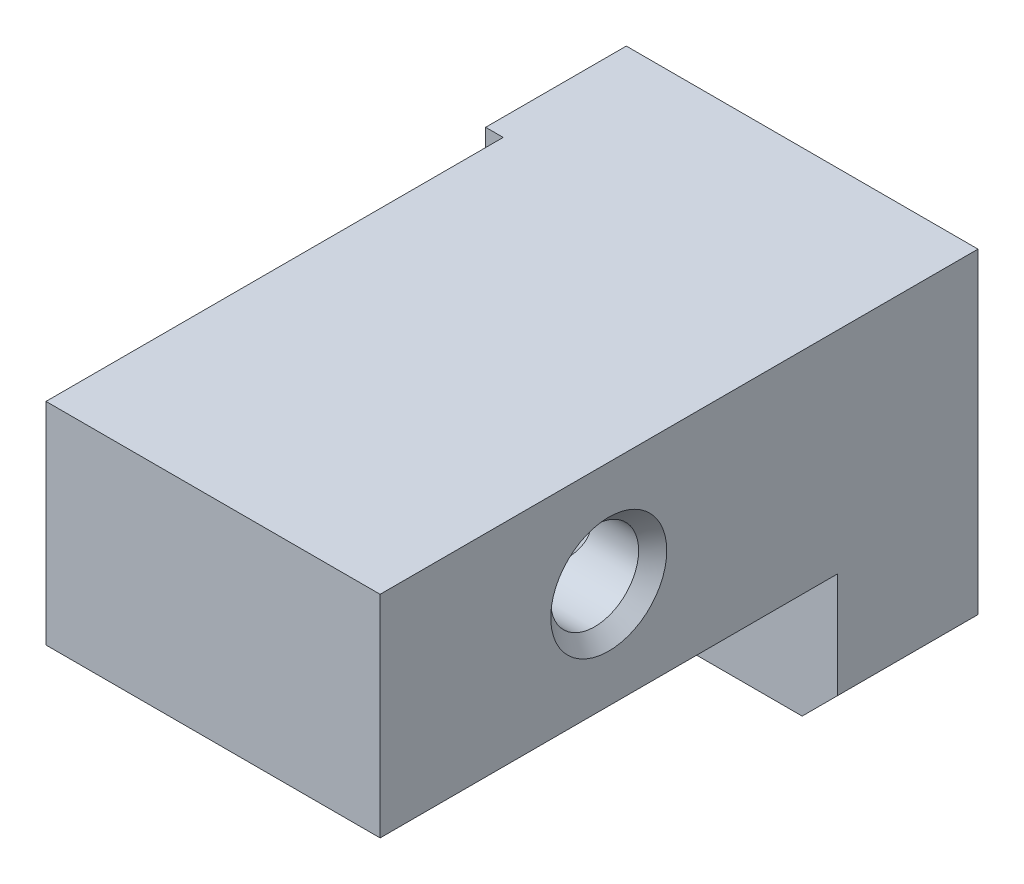
SolidWorks part; units mm, degrees
material "2024-T4"
ref_plane "Спереди" through (0, 0, 0) normal (0, 0, 1) x (1, 0, 0)
ref_plane "Сверху" through (0, 0, 0) normal (0, 1, 0) x (1, 0, 0)
ref_plane "Справа" through (0, 0, 0) normal (1, 0, 0) x (0, 0, -1)
sketch "Эскиз1" plane through (0, 0, 0) normal (0, 0, 1) x (1, 0, 0)
  line L1 (0, 0) -> (10, 0)
  line L2 (0, 0) -> (0, 10)
  line L3 (0, 10) -> (10, 10)
  line L4 (10, 0) -> (10, 10)
  dimension "D1" = 10
  dimension "D2" = 10
extrude "Бобышка-Вытянуть1" add sketch "Эскиз1" along normal blind 17
sketch "Эскиз7" plane through (0, 0, 17) normal (0, 0, 1) x (1, 0, 0)
  line L0 (0.5, 10) -> (0.5, 4)
  line L1 (10, 10) -> (0, 10) construction
  line L2 (0.5, 4) -> (10, 4)
  line L3 (10, 0) -> (10, 10) construction
  dimension "D1" = 9.5
  dimension "D2" = 6
extrude "Вырез-Вытянуть1" cut sketch "Эскиз7" against normal offset from surface (13 mm away) 4
hole_wizard "Отверстие обработанное метчиком M31" positions "Эскиз4" profile "Эскиз3" tap size "M3" standard "DIN" end condition through all
sketch "Эскиз4" plane through (10, 12.8478, -4.2017) normal (1, 0, 0) x (0, 0, 1)
  line L3 (4.2017, 2.8478) -> (4.2017, 12.8478) construction
  line L5 (21.2017, 2.8478) -> (4.2017, 2.8478) construction
  point P0 (14.7017, 5.8478)
  dimension "D1" = 10.5
  dimension "D2" = 3
sketch "Эскиз3" plane through (10, 7, 10.5) normal (0, 1, 0) x (0, 0, -1)
  line L0 (0, 0) -> (0, 9.5)
  line L1 (0, 9.5) -> (1.65, 9.5)
  line L2 (1.25, 9.1) -> (1.25, 0.4)
  line L3 (1.25, 0.4) -> (1.65, 0)
  line L5 (1.65, 0) -> (0, 0)
  line L6 (-1.25, 0.4) -> (-1.65, 0) construction
  line L7 (1.65, 9.5) -> (1.25, 9.1)
  line L8 (-1.65, 9.5) -> (-1.25, 9.1) construction
  line L11 (0, -6.35) -> (0, 107.95) construction
  dimension "Диаметр резьбы" = 2.5
  dimension "Глубина проходного сверла" = 9.5
  dimension "Диаметр передней зенковки" = 3.3
  dimension "Угол передней зенковки" = 90
  dimension "Диаметр задней зенковки" = 3.3
  dimension "Угол задней зенковки" = 90
hole_wizard "Отверстие обработанное метчиком M32" positions "Эскиз6" profile "Эскиз5" tap size "M3" standard "DIN"
sketch "Эскиз6" plane through (0, 0, 0) normal (0, 0, -1) x (-1, 0, 0)
  line L3 (0, 10) -> (0, 0) construction
  line L4 (0, 0) -> (-10, 0) construction
  point P0 (-3, 3)
  point P1 (-7, 7)
  dimension "D1" = 3
  dimension "D2" = 4
  dimension "D3" = 3
  dimension "D4" = 4
sketch "Эскиз5" plane through (3, 3, 0) normal (1, 0, 0) x (0, 1, 0)
  line L0 (0, 0) -> (0, 11.2511)
  line L1 (0, 11.2511) -> (1.25, 10.5)
  line L2 (1.25, 10.5) -> (1.25, 0.4)
  line L3 (1.25, 0.4) -> (1.65, 0)
  line L5 (1.65, 0) -> (0, 0)
  line L6 (-1.25, 0.4) -> (-1.65, 0) construction
  line L10 (0, 11.2511) -> (-1.25, 10.5) construction
  line L11 (0, -6.35) -> (0, 107.95) construction
  dimension "Диаметр сверла" = 2.5
  dimension "Глубина сверла" = 10.5
  dimension "Диаметр передней зенковки" = 3.3
  dimension "Угол передней зенковки" = 90
  dimension "Угол заточки сверла" = 118
chamfer "Фаска1" distance 1 angle 45 1 edges at (10, 0, 2)
